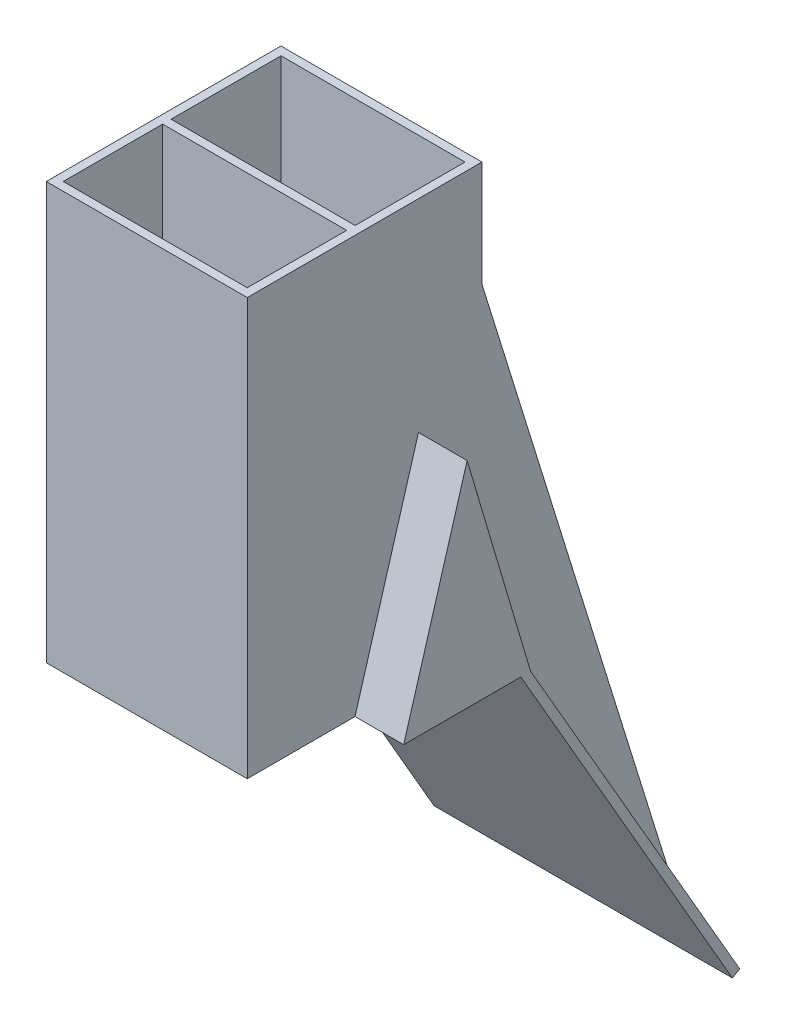
SolidWorks part; units mm, degrees
ref_plane "Ebene vorne" through (0, 0, 0) normal (0, 0, 1) x (1, 0, 0)
ref_plane "Ebene oben" through (0, 0, 0) normal (0, 1, 0) x (1, 0, 0)
ref_plane "Ebene rechts" through (0, 0, 0) normal (1, 0, 0) x (0, 0, -1)
sketch "Skizze1" plane through (0, 0, 0) normal (0, 1, 0) x (1, 0, 0)
  line L0 (0.4, 0.4) -> (0.4, 5.1)
  line L1 (0, 0) -> (9.5, 0)
  line L2 (0, 0) -> (0, 11.093)
  line L3 (0, 11.093) -> (9.5, 11.093)
  line L4 (9.5, 0) -> (9.5, 11.093)
  line L9 (0.4, 10.693) -> (9.1, 10.693)
  line L10 (9.1, 0.4) -> (9.1, 5.1)
  line L11 (0.4, 0.4) -> (9.1, 0.4)
  line L12 (0.4, 5.1) -> (9.1, 5.1)
  line L13 (9.1, 5.5) -> (0.4, 5.5)
  line L14 (0.4, 5.5) -> (0.4, 10.693)
  line L15 (0.4, 0.4) -> (0.4, 10.693) construction
  line L16 (9.1, 5.5) -> (9.1, 10.693)
  line L17 (9.1, 0.4) -> (9.1, 10.693) construction
  dimension "D1" = 11.093
  dimension "D2" = 9.5
  dimension "D3" = 0.4
  dimension "D4" = 0.4
  dimension "D5" = 5.193
extrude "Aufsatz-Linear austragen1" add sketch "Skizze1" along normal blind 19.7
sketch "Skizze2" plane through (0, 0, 0) normal (-1, 0, 0) x (0, 0, 1)
  line L1 (-11.093, 19.7) -> (-11.093, 0) construction
  line L2 (-11.093, 0) -> (-8.093, 10.13)
  line L3 (-8.093, 10.13) -> (-5.093, 0)
  line L5 (-11.093, 0) -> (0, 0) construction
  line L6 (-5.093, 0) -> (-11.093, 0)
  dimension "D1" = 10.13
  dimension "D2" = 6
  dimension "D3" = 3
extrude "Aufsatz-Linear austragen2" add sketch "Skizze2" along normal blind 2.3
ref_plane "Ebene1" through (4.75, 0, 0) normal (1, 0, 0) x (0, 0, -1)
mirror "Spiegeln1" about plane through (4.75, 0, 0) normal (1, 0, 0) of "Aufsatz-Linear austragen2"
sketch "Skizze3" plane through (-2.3, 0, 0) normal (-1, 0, 0) x (0, 0, 1)
  line L0 (-10.3797, 1) -> (-5.8063, 1)
  line L1 (-11.093, 0) -> (-5.093, 0) construction
  line L10 (-10.5574, 0.4) -> (-5.6286, 0.4)
  line L11 (-5.6286, 0.4) -> (-8.093, 8.7213)
  line L12 (-8.093, 8.7213) -> (-10.5574, 0.4)
  line L14 (-5.8063, 1) -> (-8.093, 8.7213)
  line L15 (-8.093, 8.7213) -> (-10.3797, 1)
  dimension "D1" = 0.4
  dimension "D2" = 1
extrude "Schnitt-Linear austragen1" cut sketch "Skizze3" against normal blind 13.7
sketch "Skizze4" plane through (0, 0, 0) normal (0, -1, 0) x (1, 0, 0)
  line L0 (9.1, -10.693) -> (0.4, -10.693) construction
  line L1 (-1.9, -5.5) -> (11.4, -5.5)
  line L2 (-1.9, -5.5) -> (-1.9, -10.693)
  line L3 (-1.9, -10.693) -> (11.4, -10.693)
  line L4 (11.4, -5.5) -> (11.4, -10.693)
  line L5 (0.4, -5.5) -> (9.1, -5.5) construction
  line L6 (-2.3, -11.093) -> (-2.3, -5.093) construction
  line L7 (11.8, -11.093) -> (11.8, -5.093) construction
  dimension "D1" = 0.4
  dimension "D2" = 0.4
extrude "Schnitt-Linear austragen2" cut sketch "Skizze4" against normal blind 0.4
sketch "Skizze5" plane through (-2.3, 0, 0) normal (-1, 0, 0) x (0, 0, 1)
  line L1 (-20.9775, -17.1205) -> (-20.6311, -17.3205)
  line L2 (-20.6311, -17.3205) -> (-10.6311, 0)
  line L3 (-11.093, 0) -> (-5.093, 0) construction
  line L4 (-10.6311, 0) -> (-11.093, 0)
  line L8 (-20.9775, -17.1205) -> (-11.093, 0)
  line L9 (-11.093, 19.7) -> (-11.093, 0) construction
  dimension "D1" = 150
  dimension "D2" = 20
  dimension "D4" = 0.4
extrude "Aufsatz-Linear austragen3" add sketch "Skizze5" against normal up to vertex (14.1 mm away)
sketch "Skizze6" plane through (0, 0, 0) normal (-1, 0, 0) x (0, 0, 1)
  line L0 (-20.9775, -17.1205) -> (-11.093, 0)
  line L2 (-11.093, 0) -> (-11.093, 14.7)
  line L3 (-11.093, 14.7) -> (-20.9775, -17.1205)
  dimension "D1" = 5
extrude "Aufsatz-Linear austragen4" add sketch "Skizze6" against normal up to vertex
